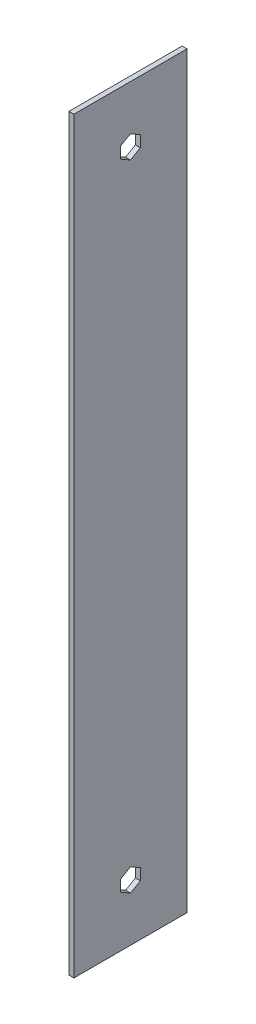
SolidWorks part; units mm, degrees
ref_plane "Front Plane" through (0, 0, 0) normal (0, 0, 1) x (1, 0, 0)
ref_plane "Top Plane" through (0, 0, 0) normal (0, 1, 0) x (1, 0, 0)
ref_plane "Right Plane" through (0, 0, 0) normal (1, 0, 0) x (0, 0, -1)
sketch "Sketch1" plane through (0, 0, 0) normal (1, 0, 0) x (0, 0, -1)
  line L0 (0, -7.3323) -> (0, -36.5125) construction
  line L1 (-36.5125, 446.0875) -> (36.5125, 446.0875)
  line L2 (-36.5125, 446.0875) -> (-36.5125, -36.5125)
  line L3 (-36.5125, -36.5125) -> (36.5125, -36.5125)
  line L4 (36.5125, 446.0875) -> (36.5125, -36.5125)
  line L5 (0, 7.3323) -> (-6.35, 3.6662)
  line L6 (-6.35, 3.6662) -> (-6.35, -3.6662)
  line L7 (-6.35, -3.6662) -> (0, -7.3323)
  line L8 (0, -7.3323) -> (6.35, -3.6662)
  line L9 (6.35, -3.6662) -> (6.35, 3.6662)
  line L10 (6.35, 3.6662) -> (0, 7.3323)
  line L11 (0, 402.2427) -> (6.35, 405.9088)
  line L12 (6.35, 405.9088) -> (6.35, 413.2412)
  line L13 (6.35, 413.2412) -> (0, 416.9073)
  line L14 (0, 416.9073) -> (-6.35, 413.2412)
  line L15 (-6.35, 413.2412) -> (-6.35, 405.9088)
  line L16 (-6.35, 405.9088) -> (0, 402.2427)
  line L17 (0, 416.9073) -> (0, 446.0875) construction
  circle A0 centre (0, 0) radius 36.5125 construction
  circle A1 centre (0, 0) radius 6.35 construction
  circle A2 centre (0, 409.575) radius 6.35 construction
  dimension "D1" = 73.025
  dimension "D3" = 12.7
  dimension "D2" = 482.6
extrude "Boss-Extrude1" add sketch "Sketch1" along normal mid plane 3.175
